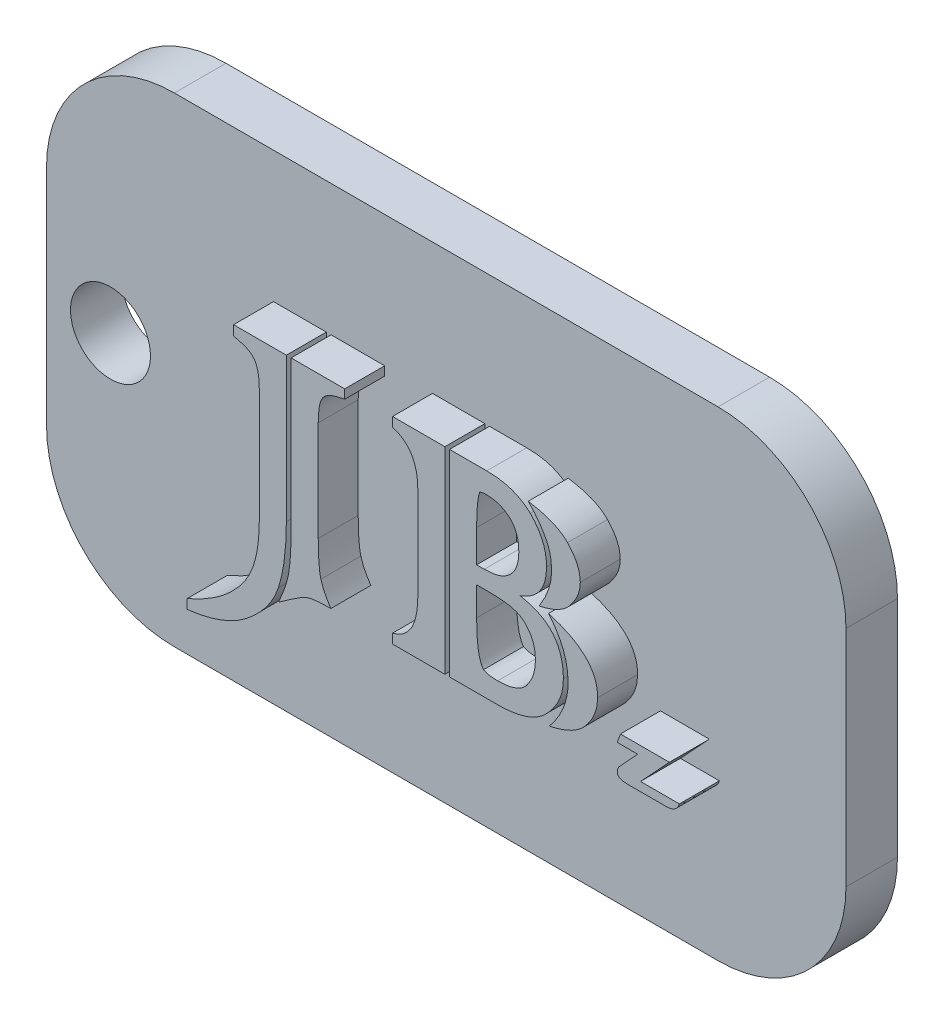
SolidWorks part; units mm, degrees
ref_plane "Front Plane" through (0, 0, 0) normal (0, 0, 1) x (1, 0, 0)
ref_plane "Top Plane" through (0, 0, 0) normal (0, 1, 0) x (1, 0, 0)
ref_plane "Right Plane" through (0, 0, 0) normal (1, 0, 0) x (0, 0, -1)
sketch "Sketch1" plane through (0, 0, 0) normal (0, 0, 1) x (1, 0, 0)
  line L0 (-30.6548, 0) -> (50.7937, 0) construction
  line L1 (0, 28.621) -> (0, -31.3988) construction
  line L3 (25, -15) -> (-25, -15)
  line L4 (25, -15) -> (25, 15)
  line L5 (25, 15) -> (-25, 15)
  line L6 (-25, -15) -> (-25, 15)
  line L7 (25, -15) -> (-25, 15) construction
  line L8 (25, 15) -> (-25, -15) construction
  point P5 (0, 0)
  dimension "D1" = 50
  dimension "D2" = 30
extrude "Boss-Extrude2" add sketch "Sketch1" along normal blind 3.2206
sketch "Sketch4" plane through (0, 0, 3.2206) normal (0, 0, 1) x (1, 0, 0)
  text T0 "JB" font "Colonna MT" height in points 48
fillet "Fillet4" radius 8 4 edges at (25, -15, 1.6103) (-25, -15, 1.6103) (-25, 15, 1.6103) (25, 15, 1.6103)
sketch "Sketch8" plane through (0, 0, 3.2206) normal (0, 0, 1) x (1, 0, 0)
  line L0 (-25, 7) -> (-25, -7) construction
  line L1 (-25, 0) -> (25, 0) construction
  line L2 (25, -7) -> (25, 7) construction
  line L3 (-21, 13.9282) -> (-21, -13.9282) construction
  circle A0 centre (-21, 0) radius 2.5
  arc A3 (-17, 15) -> (-25, 7) centre (-17, 7) ccw construction
  arc A4 (-25, -7) -> (-17, -15) centre (-17, -7) ccw construction
  dimension "D1" = 5
  dimension "D2" = 4
extrude "Cut-Extrude3" cut sketch "Sketch8" against normal through all
sketch "Sketch10" plane through (0, 0, 3.2206) normal (0, 0, 1) x (1, 0, 0)
  text T0 "z" font "Magneto" height in points 20
extrude "Boss-Extrude15" add sketch "Sketch4" along normal blind 2.5
extrude "Boss-Extrude16" add sketch "Sketch10" along normal blind 2.5
